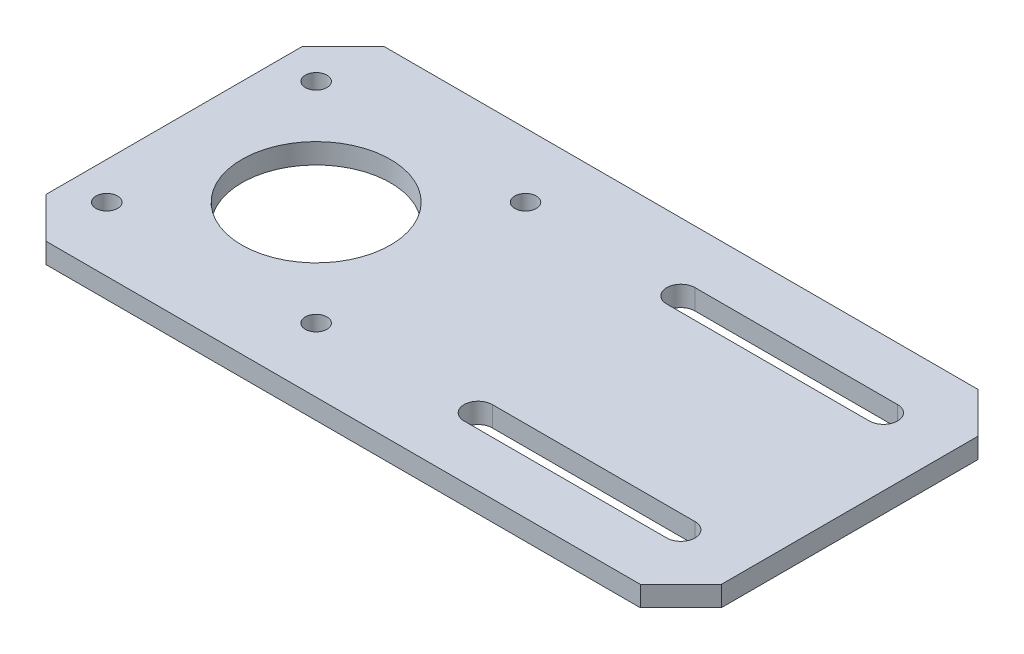
SolidWorks part; units mm, degrees
ref_plane "前视基准面" through (0, 0, 0) normal (0, 0, 1) x (1, 0, 0)
ref_plane "上视基准面" through (0, 0, 0) normal (0, 1, 0) x (1, 0, 0)
ref_plane "右视基准面" through (0, 0, 0) normal (1, 0, 0) x (0, 0, -1)
sketch "草图1" plane through (0, 0, 0) normal (0, 1, 0) x (1, 0, 0)
  line L0 (0, 25) -> (21, 25) construction
  line L1 (0, 0) -> (100, 0)
  line L2 (0, 0) -> (0, 50)
  line L3 (0, 50) -> (100, 50)
  line L4 (100, 0) -> (100, 50)
  line L5 (100, 25) -> (60.8469, 25) construction
  line L6 (5.5, 40.5) -> (36.5, 40.5) construction
  line L7 (5.5, 40.5) -> (5.5, 9.5) construction
  line L8 (5.5, 9.5) -> (36.5, 9.5) construction
  line L9 (36.5, 40.5) -> (36.5, 9.5) construction
  line L10 (5.5, 40.5) -> (36.5, 9.5) construction
  line L11 (5.5, 9.5) -> (36.5, 40.5) construction
  line L12 (60, 40) -> (90, 40) construction
  line L13 (60, 42.1) -> (90, 42.1)
  line L14 (60, 37.9) -> (90, 37.9)
  line L15 (60, 10) -> (90, 10) construction
  line L16 (60, 7.9) -> (90, 7.9)
  line L17 (60, 12.1) -> (90, 12.1)
  circle A0 centre (21, 25) radius 11
  circle A1 centre (5.5, 40.5) radius 1.6
  circle A2 centre (36.5, 40.5) radius 1.6
  circle A3 centre (36.5, 9.5) radius 1.6
  circle A4 centre (5.5, 9.5) radius 1.6
  arc A5 (60, 42.1) -> (60, 37.9) centre (60, 40) ccw
  arc A6 (90, 37.9) -> (90, 42.1) centre (90, 40) ccw
  arc A7 (60, 7.9) -> (60, 12.1) centre (60, 10) cw
  arc A8 (90, 12.1) -> (90, 7.9) centre (90, 10) cw
  point P20 (75, 40)
  point P27 (75, 10)
  dimension "D1" = 22
  dimension "D2" = 3.2
  dimension "D3" = 31
  dimension "D4" = 50
  dimension "D5" = 21
  dimension "D6" = 100
  dimension "D7" = 4.2
  dimension "D8" = 30
  dimension "D9" = 30
  dimension "D10" = 25
extrude "凸台-拉伸1" add sketch "草图1" along normal blind 3
chamfer "倒角1" distance 6 angle 45 4 edges at (0, 1.5, 0) (0, 1.5, -50) (100, 1.5, -50) (100, 1.5, 0)
